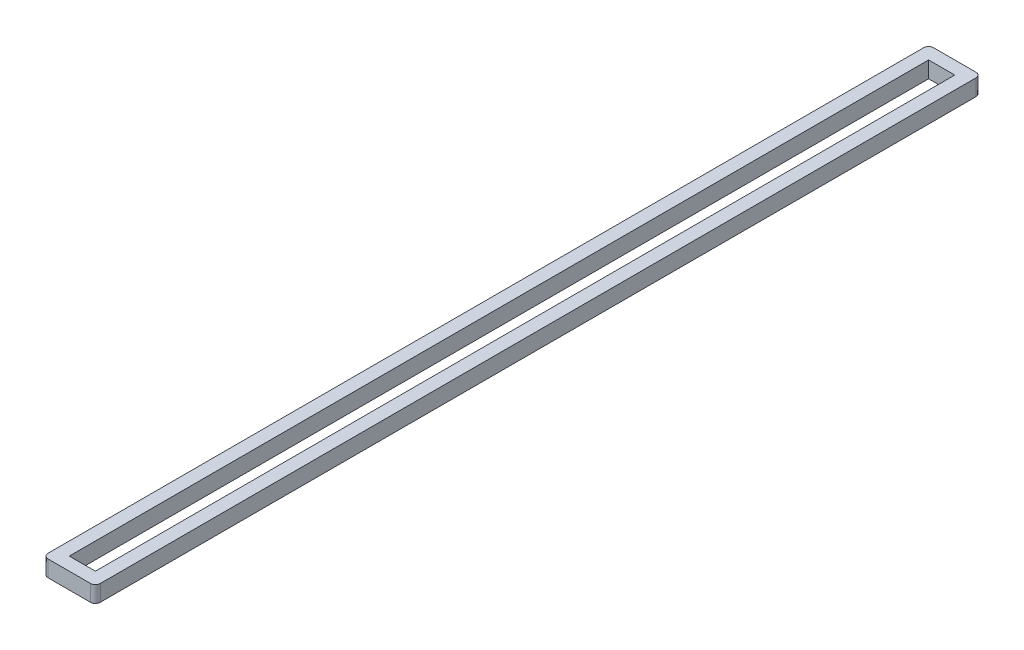
SolidWorks part; units mm, degrees
ref_plane "Front Plane" through (0, 0, 0) normal (0, 0, 1) x (1, 0, 0)
ref_plane "Top Plane" through (0, 0, 0) normal (0, 1, 0) x (1, 0, 0)
ref_plane "Right Plane" through (0, 0, 0) normal (1, 0, 0) x (0, 0, -1)
sketch "Sketch1" plane through (0, 0, 0) normal (0, 1, 0) x (1, 0, 0)
  line L1 (-8, -135.5) -> (8, -135.5)
  line L2 (-8, -135.5) -> (-8, 135.5)
  line L3 (-8, 135.5) -> (8, 135.5)
  line L4 (8, -135.5) -> (8, 135.5)
  line L5 (-8, -135.5) -> (8, 135.5) construction
  line L6 (-8, 135.5) -> (8, -135.5) construction
  line L7 (-4, -131.5) -> (4, -131.5)
  line L8 (-4, -131.5) -> (-4, 131.5)
  line L9 (-4, 131.5) -> (4, 131.5)
  line L10 (4, -131.5) -> (4, 131.5)
  line L11 (-4, -131.5) -> (4, 131.5) construction
  line L12 (-4, 131.5) -> (4, -131.5) construction
  point P0 (0, 0)
  point P6 (0, 0)
  dimension "D1" = 16
  dimension "D2" = 271
  dimension "D3" = 4
  dimension "D4" = 4
extrude "Boss-Extrude1" add sketch "Sketch1" along normal blind 5
fillet "Fillet1" radius 1.5 4 edges at (8, 2.5, 135.5) (-8, 2.5, 135.5) (-8, 2.5, -135.5) (8, 2.5, -135.5)
